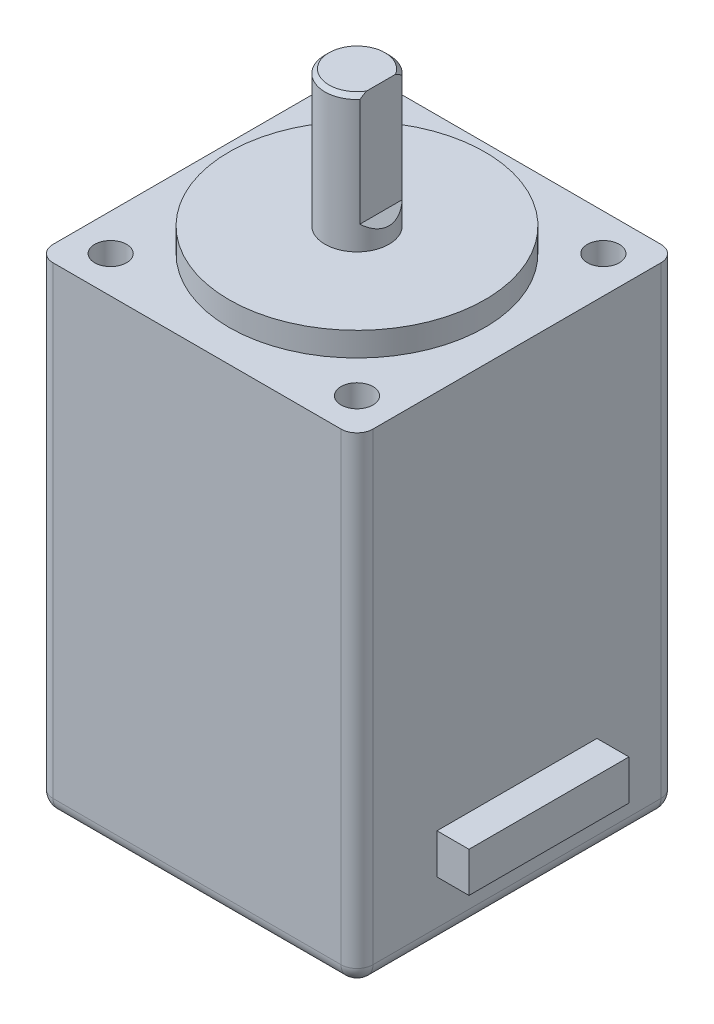
SolidWorks part; units mm, degrees
ref_plane "Front Plane" through (0, 0, 0) normal (0, 0, 1) x (1, 0, 0)
ref_plane "Top Plane" through (0, 0, 0) normal (0, 1, 0) x (1, 0, 0)
ref_plane "Right Plane" through (0, 0, 0) normal (1, 0, 0) x (0, 0, -1)
sketch "Sketch1" plane through (0, 0, 0) normal (0, 1, 0) x (1, 0, 0)
  line L1 (10, -10) -> (-10, -10)
  line L2 (10, -10) -> (10, 10)
  line L3 (10, 10) -> (-10, 10)
  line L4 (-10, -10) -> (-10, 10)
  line L5 (10, -10) -> (-10, 10) construction
  line L6 (10, 10) -> (-10, -10) construction
  point P0 (0, 0)
  dimension "D1" = 20
extrude "Boss-Extrude1" add sketch "Sketch1" against normal blind 30
sketch "Sketch2" plane through (0, 0, 0) normal (0, 1, 0) x (1, 0, 0)
  line L1 (7.7, -7.7) -> (-7.7, -7.7) construction
  line L2 (7.7, -7.7) -> (7.7, 7.7) construction
  line L3 (7.7, 7.7) -> (-7.7, 7.7) construction
  line L4 (-7.7, -7.7) -> (-7.7, 7.7) construction
  line L5 (7.7, -7.7) -> (-7.7, 7.7) construction
  line L6 (7.7, 7.7) -> (-7.7, -7.7) construction
  circle A0 centre (-7.7, 7.7) radius 1
  circle A1 centre (7.7, 7.7) radius 1
  circle A2 centre (7.7, -7.7) radius 1
  circle A3 centre (-7.7, -7.7) radius 1
  point P0 (0, 0)
  dimension "D4" = 2
  dimension "D2" = 15.4
extrude "Cut-Extrude1" cut sketch "Sketch2" against normal blind 2.5
sketch "Sketch3" plane through (0, 0, 0) normal (0, 1, 0) x (1, 0, 0)
  circle A0 centre (0, 0) radius 8
  dimension "D1" = 16
extrude "Boss-Extrude2" add sketch "Sketch3" along normal blind 1.5
sketch "Sketch4" plane through (0, 0, 0) normal (0, 1, 0) x (1, 0, 0)
  circle A0 centre (0, 0) radius 2
  dimension "D1" = 4
extrude "Boss-Extrude3" add sketch "Sketch4" along normal blind 10
sketch "Sketch5" plane through (0, 0, 0) normal (0, 0, 1) x (1, 0, 0)
  line L0 (2, 10) -> (1.5, 10)
  line L1 (2, 10) -> (-2, 10) construction
  line L2 (1.5, 10) -> (1.5, 3)
  line L3 (1.5, 3) -> (2, 2.5)
  line L4 (2, 1.5) -> (2, 10) construction
  line L5 (2, 2.5) -> (2, 10)
  dimension "D1" = 45
  dimension "D2" = 0.5
  dimension "D3" = 7.5
extrude "Cut-Extrude2" cut sketch "Sketch5" against normal through all both and the other way through all
chamfer "Chamfer1" distance 0.25 angle 45 1 edges at (-2, 10, 0)
fillet "Fillet1" radius 1 8 edges at (0, -30, 10) (10, -30, 0) (0, -30, -10) (-10, -30, 0) (-10, -15, -10) (10, -15, -10) (10, -15, 10) (-10, -15, 10)
sketch "Sketch6" plane through (0, 0, 0) normal (1, 0, 0) x (0, 0, -1)
  line L0 (0, -25) -> (0, 0) construction
  line L1 (5, -26.25) -> (-5, -26.25)
  line L2 (5, -26.25) -> (5, -23.75)
  line L3 (5, -23.75) -> (-5, -23.75)
  line L4 (-5, -26.25) -> (-5, -23.75)
  line L5 (5, -26.25) -> (-5, -23.75) construction
  line L6 (5, -23.75) -> (-5, -26.25) construction
  line L7 (9, -30) -> (-9, -30) construction
  point P0 (0, -25)
  dimension "D1" = 5
  dimension "D2" = 2.5
  dimension "D3" = 10
extrude "Boss-Extrude4" add sketch "Sketch6" along normal offset from surface (12 mm away) 2 up to face at (10, -14.5, 0) offset beyond the face yes
equation "\"D1@Sketch1\" = \"ARM Both Nema Width\""
equation "\"D1@Boss-Extrude1\"= 30.0mm"
equation "\"D2@Sketch2\" = \"ARM Both Nema Bolt Off\""
equation "\"D4@Sketch2\" = \"ARM Both Nema Bolt Size\""
equation "\"D1@Cut-Extrude1\" = \"ARM Both Nema Bolt Depth\""
equation "\"D1@Sketch3\" = \"ARM Both Nema Center Dia 1\" - 1.0mm"
equation "\"D1@Boss-Extrude2\" = \"ARM Both Nema Center Height\""
equation "\"D1@Sketch4\" = \"ARM Both Nema Shaft Dia\""
equation "\"D1@Boss-Extrude3\"= \"ARM Both Nema Shaft Length\""
equation "\"D2@Sketch5\"= \"ARM Both Nema Shaft Dia\" * ( 1 / 8 )"
equation "\"D3@Sketch5\"= \"ARM Both Nema Shaft Length\" * ( 3 / 4 )"
equation "\"D1@Chamfer1\"= \"ALL Small Fillet\" / 2"
equation "\"ALL Big Fillet\"= 10.0mm"
equation "\"ALL Medium Fillet\"= 1.0mm"
equation "\"ALL Small Fillet\"= 0.5mm"
equation "\"BODY Rad\"= 82.5mm"
equation "\"BODY End Cut Rad\"= 72.5mm"
equation "\"BODY Height Ext\"= 27.5mm"
equation "\"BODY Bottom Cut Dist\"= 50.0mm"
equation "\"BODY Seal Thickness\"= 3.75mm"
equation "\"BODY Wall Extra Thickness\"= 2.5mm"
equation "\"BODY Bottom Extra Nut Wall\"= 7.5mm"
equation "\"ARM Both Dia\"= 39.75mm"
equation "\"ARM Both Length\"= 67.5mm"
equation "\"ARM Both Wire Hole Dia\"= 15.0mm"
equation "\"ARM Both Prop Seal Thickness\"= 2.5mm"
equation "\"ARM Both Brass Insert Dia\"= 4.875mm"
equation "\"ARM Both Bolt Cut Depth\"= 12.5mm"
equation "\"ARM Both Nema Bolt Off\"= 15.4mm"
equation "\"ARM Both Nema Bolt Depth\"= 2.5mm"
equation "\"ARM Both Nema Width\"= 20.0mm"
equation "\"ARM Both Nema Wall Off\"= 2.5mm"
equation "\"ARM Both Nema Center Dia 1\"= 17.0mm"
equation "\"ARM Both Nema Center Dia 2\"= 10.0mm"
equation "\"ARM Both Nema Bearing OD\"= 16.0mm"
equation "\"ARM Both Nema Bearing ID\"= 10.0mm"
equation "\"ARM Both Nema Bearing Thickness\"= 4.0mm"
equation "\"ARM Both Nema Height\"= 38.0mm"
equation "\"ARM Both Nema Shaft Dia\"= 4.0mm"
equation "\"ARM Both Nema Shaft Length\"= 10.0mm"
equation "\"ARM Both Nema Center Height\"= 1.5mm"
equation "\"ARM Rotating Bearing OD\"= 68.0mm"
equation "\"ARM Rotating Bearing ID\"= 40.0mm"
equation "\"ARM Rotating Bearing Thickness\"= 15.0mm"
equation "\"ARM Static Mount Dia\"= 65.0mm"
equation "\"ARM Static Bolt Off\"= 1.125mm"
equation "\"ALL Bolt Hole Off\"= 0.25mm"
equation "\"ALL Vert Bolt Hole Off Scalar\"= 0.5mm"
equation "\"ALL Horz Bolt Hole Off Scalar\"= 1.25mm"
equation "\"ALL Nut Size Off\"= 0.25mm"
equation "\"ALL Vert Nut Off Scalar\"= 0.5mm"
equation "\"ALL Horz Nut Off Scalar\"= 1.25mm"
equation "\"BODY Bolt Count\"= 12"
equation "\"BODY Bolt Size\"= 6"
equation "\"BODY Bolt Length\"= 22.0mm"
equation "\"BODY Bolt Head Dia\"= IIF ( \"BODY Bolt Size\" = 3 , 5.75mm , IIF ( \"BODY Bolt Size\" = 4 , 7.25mm , IIF ( \"BODY Bolt Size\" = 5 , 8.75mm , IIF ( \"BODY Bolt Size\" = 6 , 10.25mm , 5.75mm ) ) ) )"
equation "\"BODY Bolt Head Height\"= IIF ( \"BODY Bolt Size\" = 3 , 3.0mm , IIF ( \"BODY Bolt Size\" = 4 , 4.0mm , IIF ( \"BODY Bolt Size\" = 5 , 5.0mm , IIF ( \"BODY Bolt Size\" = 6 , 6.0mm , 3.0mm ) ) ) )"
equation "\"BODY Nut Width\"= IIF ( \"BODY Bolt Size\" = 3 , 5.5mm , IIF ( \"BODY Bolt Size\" = 4 , 7.0mm , IIF ( \"BODY Bolt Size\" = 5 , 8.0mm , IIF ( \"BODY Bolt Size\" = 6 , 10.0mm , 5.5mm ) ) ) )"
equation "\"BODY Nut Height\"= IIF ( \"BODY Bolt Size\" = 3 , 4.0mm , IIF ( \"BODY Bolt Size\" = 4 , 5.0mm , IIF ( \"BODY Bolt Size\" = 5 , 5.0mm , IIF ( \"BODY Bolt Size\" = 6 , 6.0mm , 4.0mm ) ) ) )"
equation "\"ARM Static Bolt Count\"= 8"
equation "\"ARM Static Bolt Size\"= 5"
equation "\"ARM Static Bolt Length\"= 20.0mm"
equation "\"ARM Static Bolt Head Dia\"= IIF ( \"ARM Static Bolt Size\" = 3 , 5.75mm , IIF ( \"ARM Static Bolt Size\" = 4 , 7.25mm , IIF ( \"ARM Static Bolt Size\" = 5 , 8.75mm , IIF ( \"ARM Static Bolt Size\" = 6 , 10.25mm , 5.75mm ) ) ) )"
equation "\"ARM Static Bolt Head Height\"= IIF ( \"ARM Static Bolt Size\" = 3 , 3.0mm , IIF ( \"ARM Static Bolt Size\" = 4 , 4.0mm , IIF ( \"ARM Static Bolt Size\" = 5 , 5.0mm , IIF ( \"ARM Static Bolt Size\" = 6 , 6.0mm , 3.0mm ) ) ) )"
equation "\"ARM Static Nut Width\"= IIF ( \"ARM Static Bolt Size\" = 3 , 5.5mm , IIF ( \"ARM Static Bolt Size\" = 4 , 7.0mm , IIF ( \"ARM Static Bolt Size\" = 5 , 8.0mm , IIF ( \"ARM Static Bolt Size\" = 6 , 10.0mm , 5.5mm ) ) ) )"
equation "\"ARM Static Nut Height\"= IIF ( \"ARM Static Bolt Size\" = 3 , 4.0mm , IIF ( \"ARM Static Bolt Size\" = 4 , 5.0mm , IIF ( \"ARM Static Bolt Size\" = 5 , 5.0mm , IIF ( \"ARM Static Bolt Size\" = 6 , 6.0mm , 4.0mm ) ) ) )"
equation "\"ARM Gear Width Off\"= 2.5mm"
equation "\"ARM Gear Bolt Count\"= 4"
equation "\"ARM Gear Rotation\"= 360.0deg"
equation "\"ARM Gear Bolt Size\"= 3"
equation "\"ARM Gear Bolt Length\"= 20.0mm"
equation "\"ARM Gear Bolt Head Dia\"= IIF ( \"ARM Static Bolt Size\" = 3 , 5.75mm , IIF ( \"ARM Static Bolt Size\" = 4 , 7.25mm , IIF ( \"ARM Static Bolt Size\" = 5 , 8.75mm , IIF ( \"ARM Static Bolt Size\" = 6 , 10.25mm , 5.75mm ) ) ) )"
equation "\"ARM Gear Bolt Head Height\"= IIF ( \"ARM Static Bolt Size\" = 3 , 3.0mm , IIF ( \"ARM Static Bolt Size\" = 4 , 4.0mm , IIF ( \"ARM Static Bolt Size\" = 5 , 5.0mm , IIF ( \"ARM Static Bolt Size\" = 6 , 6.0mm , 3.0mm ) ) ) )"
equation "\"ARM Gear Nut Width\"= IIF ( \"ARM Static Bolt Size\" = 3 , 5.5mm , IIF ( \"ARM Static Bolt Size\" = 4 , 7.0mm , IIF ( \"ARM Static Bolt Size\" = 5 , 8.0mm , IIF ( \"ARM Static Bolt Size\" = 6 , 10.0mm , 5.5mm ) ) ) )"
equation "\"ARM Gear Nut Height\"= IIF ( \"ARM Static Bolt Size\" = 3 , 4.0mm , IIF ( \"ARM Static Bolt Size\" = 4 , 5.0mm , IIF ( \"ARM Static Bolt Size\" = 5 , 5.0mm , IIF ( \"ARM Static Bolt Size\" = 6 , 6.0mm , 4.0mm ) ) ) )"
equation "\"ARM Both Prop Plate Bolt Size\"= 3"
equation "\"ARM Both Prop Plate Bolt Length\"= 16.0mm"
equation "\"ARM Both Prop Plate Bolt Head Dia\"= IIF ( \"ARM Both Prop Plate Bolt Size\" = 3 , 5.75mm , IIF ( \"ARM Both Prop Plate Bolt Size\" = 4 , 7.25mm , IIF ( \"ARM Both Prop Plate Bolt Size\" = 5 , 8.75mm , IIF ( \"ARM Both Prop Plate Bolt Size\" = 6 , 10.25mm , 5.75mm ) ) ) )"
equation "\"ARM Both Prop Plate Bolt Head Height\"= IIF ( \"ARM Both Prop Plate Bolt Size\" = 3 , 3.0mm , IIF ( \"ARM Both Prop Plate Bolt Size\" = 4 , 4.0mm , IIF ( \"ARM Both Prop Plate Bolt Size\" = 5 , 5.0mm , IIF ( \"ARM Both Prop Plate Bolt Size\" = 6 , 6.0mm , 3.0mm ) ) ) )"
equation "\"ARM Both Nema Bolt Size\"= 2"
equation "\"ARM Both Nema Bolt Head Dia\"= IIF ( \"ARM Both Nema Bolt Size\" = 3 , 5.75mm , IIF ( \"ARM Both Nema Bolt Size\" = 4 , 7.25mm , IIF ( \"ARM Both Nema Bolt Size\" = 5 , 8.75mm , IIF ( \"ARM Both Nema Bolt Size\" = 6 , 10.25mm , 5.75mm ) ) ) )"
equation "\"ARM Both Nema Bolt Head Height\"= IIF ( \"ARM Both Nema Bolt Size\" = 3 , 3.0mm , IIF ( \"ARM Both Nema Bolt Size\" = 4 , 4.0mm , IIF ( \"ARM Both Nema Bolt Size\" = 5 , 5.0mm , IIF ( \"ARM Both Nema Bolt Size\" = 6 , 6.0mm , 3.0mm ) ) ) )"
